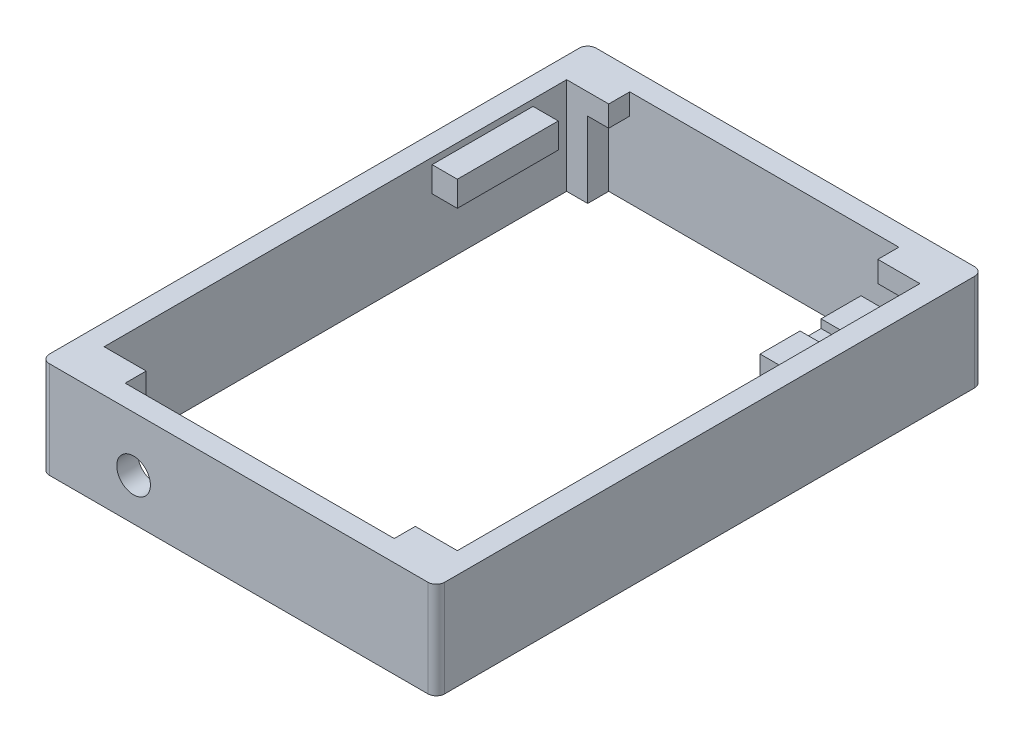
SolidWorks part; units mm, degrees
ref_plane "Front Plane" through (0, 0, 0) normal (0, 0, 1) x (1, 0, 0)
ref_plane "Top Plane" through (0, 0, 0) normal (0, 1, 0) x (1, 0, 0)
ref_plane "Right Plane" through (0, 0, 0) normal (1, 0, 0) x (0, 0, -1)
sketch "Sketch1" plane through (0, 0, 0) normal (0, 1, 0) x (1, 0, 0)
  line L0 (79, 125) -> (79, 120)
  line L1 (0, 0) -> (94, 0)
  line L2 (0, 0) -> (0, 130)
  line L3 (0, 130) -> (94, 130)
  line L4 (94, 0) -> (94, 130)
  line L5 (79, 120) -> (89, 120)
  line L6 (89, 120) -> (89, 10)
  line L7 (89, 10) -> (79, 10)
  line L8 (79, 10) -> (79, 5)
  line L9 (79, 5) -> (15, 5)
  line L10 (15, 5) -> (15, 10)
  line L11 (15, 10) -> (5, 10)
  line L12 (5, 10) -> (5, 120)
  line L13 (5, 120) -> (15, 120)
  line L14 (15, 120) -> (15, 125)
  line L15 (15, 125) -> (79, 125)
  point P17 (0, 0)
  point P18 (0, 0)
  point P19 (0, 0)
  point P20 (79, 122.5)
  point P21 (15, 122.5)
  point P22 (0, 0)
  point P23 (0, 0)
  dimension "D1" = 130
  dimension "D2" = 94
  dimension "D3" = 5
  dimension "D4" = 5
  dimension "D5" = 5
  dimension "D6" = 5
  dimension "D7" = 10
  dimension "D8" = 5
  dimension "D9" = 10
  dimension "D11" = 5
extrude "Boss-Extrude1" add sketch "Sketch1" along normal blind 23
sketch "Sketch3" plane through (5, 0, 0) normal (1, 0, 0) x (0, 0, -1)
  line L0 (120, 23) -> (10, 23) construction
  line L1 (112, 21.5) -> (88, 21.5)
  line L2 (112, 21.5) -> (112, 15.5)
  line L3 (112, 15.5) -> (88, 15.5)
  line L4 (88, 21.5) -> (88, 15.5)
  line L5 (120, 23) -> (120, 0) construction
  point P6 (112, 18.5)
  dimension "D1" = 24
  dimension "D2" = 6
  dimension "D3" = 1.5
  dimension "D4" = 8
extrude "Boss-Extrude2" add sketch "Sketch3" along normal blind 6
ref_plane "Plane1" through (47, 0, 0) normal (-1, 0, 0) x (0, 0, 1)
mirror "Mirror3" about plane through (47, 0, 0) normal (-1, 0, 0) of "Boss-Extrude2"
sketch "Sketch4" plane through (0, 21.5, 0) normal (0, 1, 0) x (1, 0, 0)
  line L0 (83, 112) -> (83, 88) construction
  line L1 (83, 102.5) -> (89, 102.5)
  line L2 (83, 102.5) -> (83, 97.5)
  line L3 (83, 97.5) -> (89, 97.5)
  line L4 (89, 102.5) -> (89, 97.5)
  line L5 (89, 112) -> (89, 88) construction
  point P4 (83, 100)
  point P7 (83, 100)
  dimension "D1" = 5
extrude "Cut-Extrude1" cut sketch "Sketch4" against normal blind 2
sketch "Sketch5" plane through (0, 0, 0) normal (0, -1, 0) x (1, 0, 0)
  line L0 (79, -120) -> (79, -125) construction
  line L1 (84, -125) -> (79, -125)
  line L2 (84, -125) -> (84, -120)
  line L3 (84, -120) -> (79, -120)
  line L4 (79, -125) -> (79, -120)
  line L5 (89, -120) -> (79, -120) construction
  line L6 (79, -125) -> (15, -125) construction
  dimension "D1" = 5
extrude "Cut-Extrude2" cut sketch "Sketch5" against normal blind 18
pattern_linear "LPattern1" count 2 spacing 69 along (-1, 0, 0) count 2 spacing 115 along (0, 0, 1) of "Cut-Extrude2"
fillet "Fillet1" radius 2 4 edges at (0, 11.5, 0) (94, 11.5, 0) (94, 11.5, -130) (0, 11.5, -130)
sketch "Sketch6" plane through (0, 0, 0) normal (0, 0, 1) x (1, 0, 0)
  line L0 (2, 0) -> (92, 0) construction
  line L1 (2, 23) -> (2, 0) construction
  circle A0 centre (22, 10) radius 4
  dimension "D1" = 8
  dimension "D2" = 10
  dimension "D3" = 20
extrude "Cut-Extrude3" cut sketch "Sketch6" against normal blind 7
